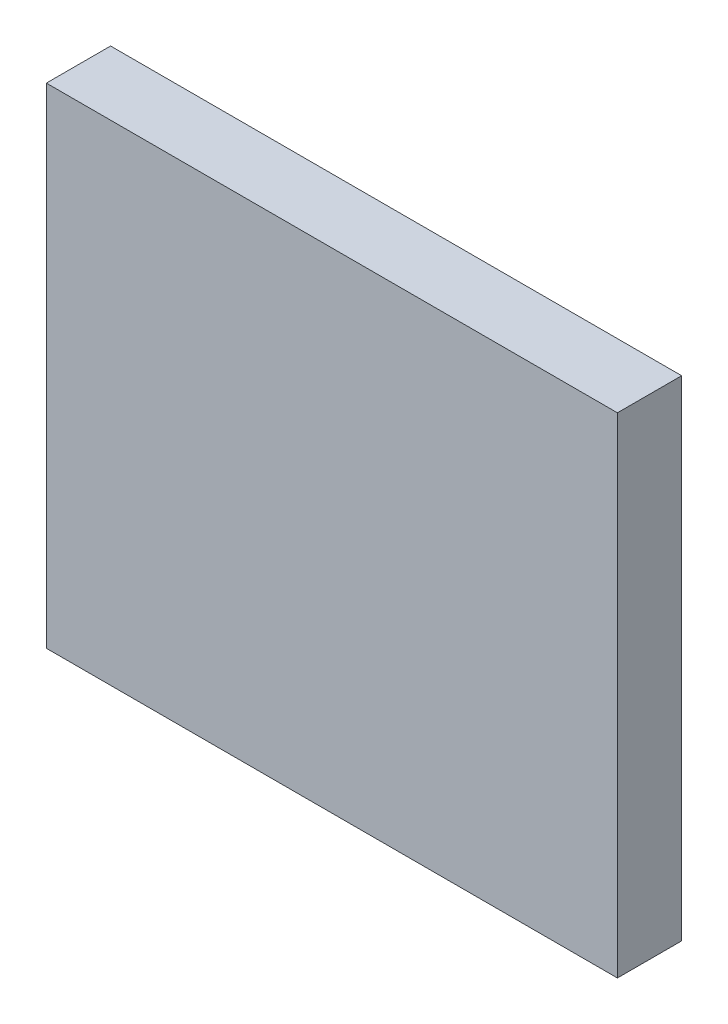
SolidWorks part; units mm, degrees
ref_plane "Front Plane" through (0, 0, 0) normal (0, 0, 1) x (1, 0, 0)
ref_plane "Top Plane" through (0, 0, 0) normal (0, 1, 0) x (1, 0, 0)
ref_plane "Right Plane" through (0, 0, 0) normal (1, 0, 0) x (0, 0, -1)
sketch "Sketch1" plane through (0, 0, 0) normal (0, 0, 1) x (1, 0, 0)
  line L0 (-4.445, 3.81) -> (4.445, 3.81)
  line L1 (4.445, 3.81) -> (4.445, -3.81)
  line L2 (4.445, -3.81) -> (-4.445, -3.81)
  line L3 (-4.445, -3.81) -> (-4.445, 3.81)
extrude "Component_Outline" add sketch "Sketch1" along normal blind 1 separate body
sketch3d "3DSketch1"
  line L0 (0, 0, 0) -> (1, 0, 0)
  line L1 (0, 0, 0) -> (0, 1, 0)
  line L2 (0, 0, 0) -> (0, 0, 1)
  point P0 (0, 0, 0)
